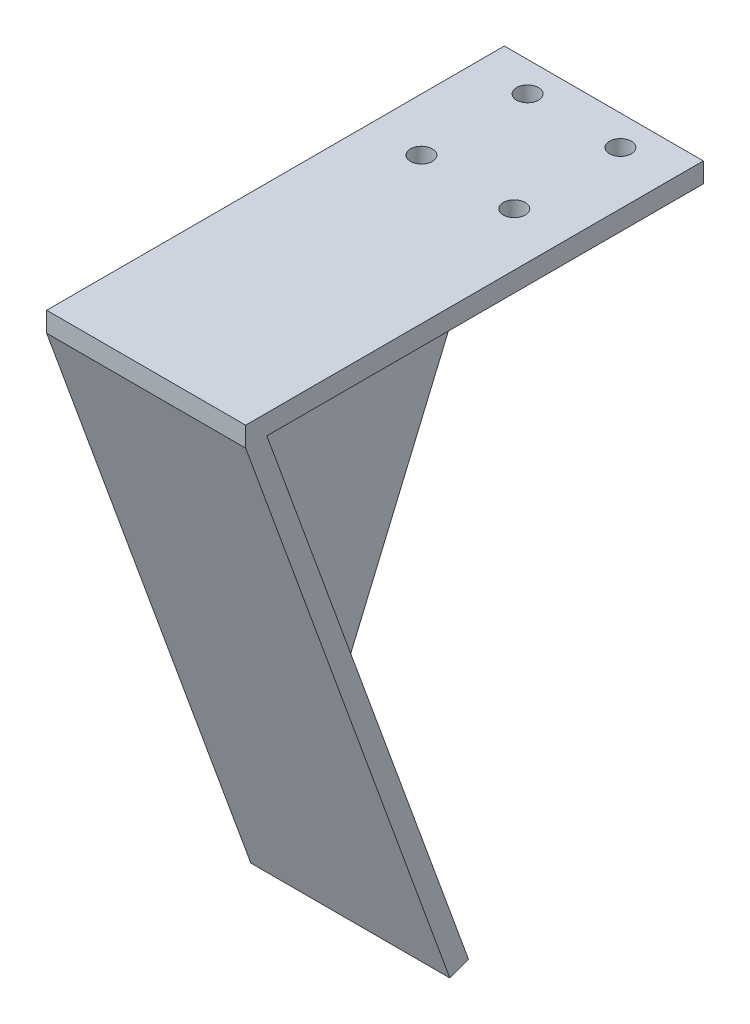
SolidWorks part; units mm, degrees
ref_plane "Front Plane" through (0, 0, 0) normal (0, 0, 1) x (1, 0, 0)
ref_plane "Top Plane" through (0, 0, 0) normal (0, 1, 0) x (1, 0, 0)
ref_plane "Right Plane" through (0, 0, 0) normal (1, 0, 0) x (0, 0, -1)
sketch "Sketch1" plane through (0, 0, 0) normal (0, 1, 0) x (1, 0, 0)
  line L2 (15, -28) -> (15, 30)
  line L3 (15, 30) -> (-15, 30)
  line L4 (-15, -28) -> (-15, 30)
  line L6 (-15, -28) -> (-15, -31)
  line L8 (-15, -31) -> (15, -31)
  line L9 (15, -28) -> (15, -31)
  point P0 (0, 0)
extrude "Boss-Extrude1" add sketch "Sketch1" along normal blind 3
sketch "Sketch2" plane through (0, 3, 0) normal (0, 1, 0) x (1, 0, 0)
  circle A1 centre (-7, 25.5) radius 1.65
  circle A2 centre (7, 25.5) radius 1.65
  circle A3 centre (-7, 9.5) radius 1.65
  circle A4 centre (7, 9.5) radius 1.65
extrude "Cut-Extrude1" cut sketch "Sketch2" against normal blind 4
sketch "Sketch3" plane through (0, 0, 31) normal (0, 0, 1) x (1, 0, 0)
  line L4 (-15, 0) -> (15, 0)
  line L5 (15, 0) -> (15, 3)
  line L6 (15, 3) -> (-15, 3)
  line L7 (-15, 3) -> (-15, 0)
  line L8 (-15, 0) -> (15, 0)
  line L9 (15, 0) -> (15, 3)
  line L10 (15, 3) -> (-15, 3)
  line L11 (-15, 3) -> (-15, 0)
  dimension "D1" = 0
extrude "Boss-Extrude2" add sketch "Sketch3" along normal blind 8
sketch "Sketch5" plane through (-15, 0, 0) normal (-1, 0, 0) x (0, 0, 1)
  line L0 (39, 0) -> (8.2182, -84.5723)
  line L1 (-30, 0) -> (39, 0) construction
  line L2 (8.2182, -84.5723) -> (5.3991, -83.5463)
  line L3 (5.3991, -83.5463) -> (35.8075, 0)
  line L4 (35.8075, 0) -> (39, 0)
  dimension "D1" = 70
extrude "Boss-Extrude3" add sketch "Sketch5" against normal up to surface (30 mm away) up to face at (15, 1.5, 4.5)
sketch "Sketch6" plane through (-15, 0, 0) normal (-1, 0, 0) x (0, 0, 1)
  line L0 (5.3991, -83.5463) -> (-30, 0)
  line L7 (-30, 0) -> (35.8075, 0)
  line L8 (35.8075, 0) -> (5.3991, -83.5463)
  line L9 (5.3991, -83.5463) -> (8.2182, -84.5723)
  line L10 (8.2182, -84.5723) -> (39, 0)
  line L11 (39, 0) -> (39, 3)
  line L12 (39, 3) -> (-30, 3)
  line L13 (-30, 3) -> (-30, 0)
  line L16 (5.3991, -83.5463) -> (8.2182, -84.5723)
  line L17 (8.2182, -84.5723) -> (39, 0)
  line L18 (39, 0) -> (39, 3)
  line L19 (39, 3) -> (-30, 3)
  line L20 (-30, 3) -> (-30, 0)
  dimension "D1" = 0
extrude "Boss-Extrude4" add sketch "Sketch6" against normal blind 3
